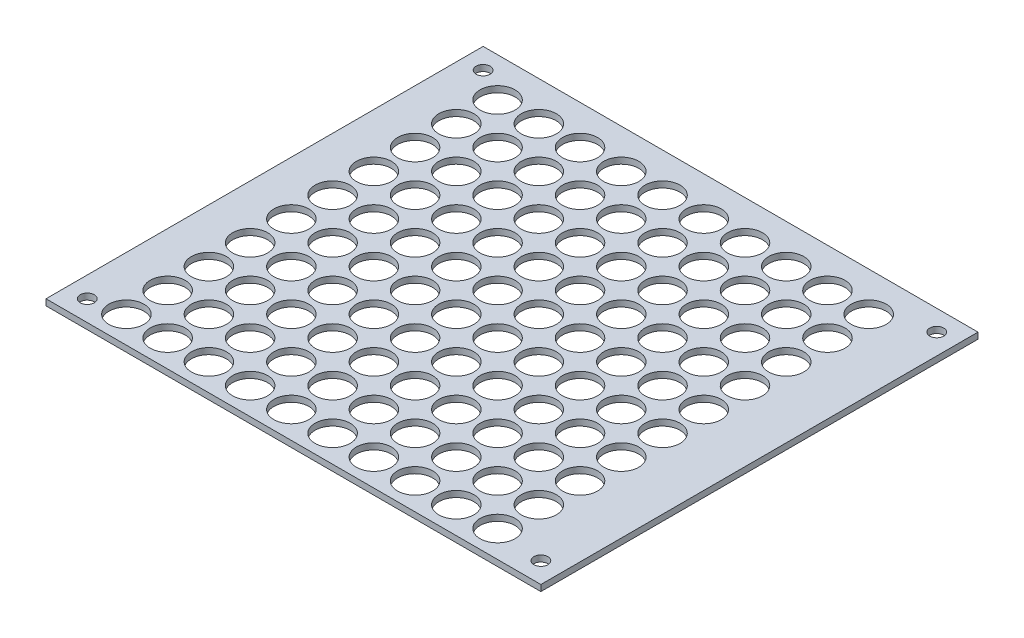
SolidWorks part; units mm, degrees
ref_plane "Front Plane" through (0, 0, 0) normal (0, 0, 1) x (1, 0, 0)
ref_plane "Top Plane" through (0, 0, 0) normal (0, 1, 0) x (1, 0, 0)
ref_plane "Right Plane" through (0, 0, 0) normal (1, 0, 0) x (0, 0, -1)
sketch "Sketch1" plane through (0, 0, 0) normal (0, 1, 0) x (1, 0, 0)
  line L0 (115, 101) -> (5, 101) construction
  line L1 (0, 0) -> (120, 0)
  line L2 (0, 0) -> (0, 106)
  line L3 (0, 106) -> (120, 106)
  line L4 (120, 0) -> (120, 106)
  line L6 (115, 101) -> (115, 5) construction
  circle A17 centre (13, 36.5) radius 4.25
  circle A18 centre (23, 36.5) radius 4.25
  circle A19 centre (13, 6.5) radius 4.25
  circle A28 centre (5, 5) radius 1.7
  circle A29 centre (5, 101) radius 1.7
  circle A30 centre (115, 101) radius 1.7
  circle A31 centre (115, 5) radius 1.7
  circle A32 centre (23, 6.5) radius 4.25
  circle A33 centre (33, 6.5) radius 4.25
  circle A34 centre (23, 16.5) radius 4.25
  circle A35 centre (33, 16.5) radius 4.25
  circle A36 centre (23, 26.5) radius 4.25
  circle A37 centre (33, 26.5) radius 4.25
  circle A38 centre (13, 16.5) radius 4.25
  circle A39 centre (13, 26.5) radius 4.25
  circle A40 centre (33, 36.5) radius 4.25
  circle A41 centre (13, 46.5) radius 4.25
  circle A42 centre (23, 46.5) radius 4.25
  circle A43 centre (33, 46.5) radius 4.25
  circle A44 centre (13, 56.5) radius 4.25
  circle A45 centre (23, 56.5) radius 4.25
  circle A46 centre (33, 56.5) radius 4.25
  circle A47 centre (13, 66.5) radius 4.25
  circle A48 centre (23, 66.5) radius 4.25
  circle A49 centre (33, 66.5) radius 4.25
  circle A50 centre (13, 76.5) radius 4.25
  circle A51 centre (23, 76.5) radius 4.25
  circle A52 centre (33, 76.5) radius 4.25
  circle A53 centre (13, 86.5) radius 4.25
  circle A54 centre (23, 86.5) radius 4.25
  circle A55 centre (33, 86.5) radius 4.25
  circle A56 centre (13, 96.5) radius 4.25
  circle A57 centre (23, 96.5) radius 4.25
  circle A58 centre (33, 96.5) radius 4.25
  circle A59 centre (43, 6.5) radius 4.25
  circle A60 centre (53, 6.5) radius 4.25
  circle A61 centre (63, 6.5) radius 4.25
  circle A62 centre (73, 6.5) radius 4.25
  circle A63 centre (83, 6.5) radius 4.25
  circle A64 centre (93, 6.5) radius 4.25
  circle A65 centre (103, 6.5) radius 4.25
  circle A66 centre (43, 16.5) radius 4.25
  circle A67 centre (53, 16.5) radius 4.25
  circle A68 centre (63, 16.5) radius 4.25
  circle A69 centre (73, 16.5) radius 4.25
  circle A70 centre (83, 16.5) radius 4.25
  circle A71 centre (93, 16.5) radius 4.25
  circle A72 centre (103, 16.5) radius 4.25
  circle A73 centre (43, 26.5) radius 4.25
  circle A74 centre (53, 26.5) radius 4.25
  circle A75 centre (63, 26.5) radius 4.25
  circle A76 centre (73, 26.5) radius 4.25
  circle A77 centre (83, 26.5) radius 4.25
  circle A78 centre (93, 26.5) radius 4.25
  circle A79 centre (103, 26.5) radius 4.25
  circle A80 centre (43, 36.5) radius 4.25
  circle A81 centre (53, 36.5) radius 4.25
  circle A82 centre (63, 36.5) radius 4.25
  circle A83 centre (73, 36.5) radius 4.25
  circle A84 centre (83, 36.5) radius 4.25
  circle A85 centre (93, 36.5) radius 4.25
  circle A86 centre (103, 36.5) radius 4.25
  circle A87 centre (43, 46.5) radius 4.25
  circle A88 centre (53, 46.5) radius 4.25
  circle A89 centre (63, 46.5) radius 4.25
  circle A90 centre (73, 46.5) radius 4.25
  circle A91 centre (83, 46.5) radius 4.25
  circle A92 centre (93, 46.5) radius 4.25
  circle A93 centre (103, 46.5) radius 4.25
  circle A94 centre (43, 56.5) radius 4.25
  circle A95 centre (53, 56.5) radius 4.25
  circle A96 centre (63, 56.5) radius 4.25
  circle A97 centre (73, 56.5) radius 4.25
  circle A98 centre (83, 56.5) radius 4.25
  circle A99 centre (93, 56.5) radius 4.25
  circle A100 centre (103, 56.5) radius 4.25
  circle A101 centre (43, 66.5) radius 4.25
  circle A102 centre (53, 66.5) radius 4.25
  circle A103 centre (63, 66.5) radius 4.25
  circle A104 centre (73, 66.5) radius 4.25
  circle A105 centre (83, 66.5) radius 4.25
  circle A106 centre (93, 66.5) radius 4.25
  circle A107 centre (103, 66.5) radius 4.25
  circle A108 centre (43, 76.5) radius 4.25
  circle A109 centre (53, 76.5) radius 4.25
  circle A110 centre (63, 76.5) radius 4.25
  circle A111 centre (73, 76.5) radius 4.25
  circle A112 centre (83, 76.5) radius 4.25
  circle A113 centre (93, 76.5) radius 4.25
  circle A114 centre (103, 76.5) radius 4.25
  circle A115 centre (43, 86.5) radius 4.25
  circle A116 centre (53, 86.5) radius 4.25
  circle A117 centre (63, 86.5) radius 4.25
  circle A118 centre (73, 86.5) radius 4.25
  circle A119 centre (83, 86.5) radius 4.25
  circle A120 centre (93, 86.5) radius 4.25
  circle A121 centre (103, 86.5) radius 4.25
  circle A122 centre (43, 96.5) radius 4.25
  circle A123 centre (53, 96.5) radius 4.25
  circle A124 centre (63, 96.5) radius 4.25
  circle A125 centre (73, 96.5) radius 4.25
  circle A126 centre (83, 96.5) radius 4.25
  circle A127 centre (93, 96.5) radius 4.25
  circle A128 centre (103, 96.5) radius 4.25
  point P7 (115, 53)
  point P9 (60, 101)
  point P10 (60, 106)
  point P20 (120, 53)
  dimension "D5" = 110
  dimension "D6" = 96
  dimension "D3" = 8.5
  dimension "D8" = 3.4
  dimension "D1" = 120
  dimension "D2" = 106
  dimension "D4" = 8
  dimension "D7" = 1.5
  dimension "D9" = 10
  dimension "D10" = 10
extrude "Boss-Extrude1" add sketch "Sketch1" along normal blind 1.5
equation "\"o\"= 10mm"
equation "\"P\"= 10"
